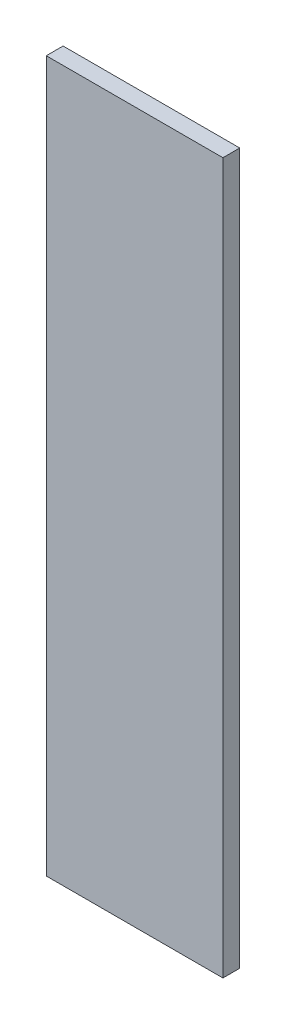
SolidWorks part; units mm, degrees
ref_plane "Front Plane" through (0, 0, 0) normal (0, 0, 1) x (1, 0, 0)
ref_plane "Top Plane" through (0, 0, 0) normal (0, 1, 0) x (1, 0, 0)
ref_plane "Right Plane" through (0, 0, 0) normal (1, 0, 0) x (0, 0, -1)
sketch "Sketch1" plane through (0, 0, 0) normal (0, 0, 1) x (1, 0, 0)
  line L1 (94.5, -380) -> (-94.5, -380)
  line L2 (94.5, -380) -> (94.5, 380)
  line L3 (94.5, 380) -> (-94.5, 380)
  line L4 (-94.5, -380) -> (-94.5, 380)
  line L5 (94.5, -380) -> (-94.5, 380) construction
  line L6 (94.5, 380) -> (-94.5, -380) construction
  point P0 (0, 0)
  dimension "D1" = 760
  dimension "D2" = 189
extrude "Boss-Extrude1" add sketch "Sketch1" along normal blind 18
equation "\"H_DSP\"=18"
equation "\"D1@Boss-Extrude1\"=\"H_DSP\""
